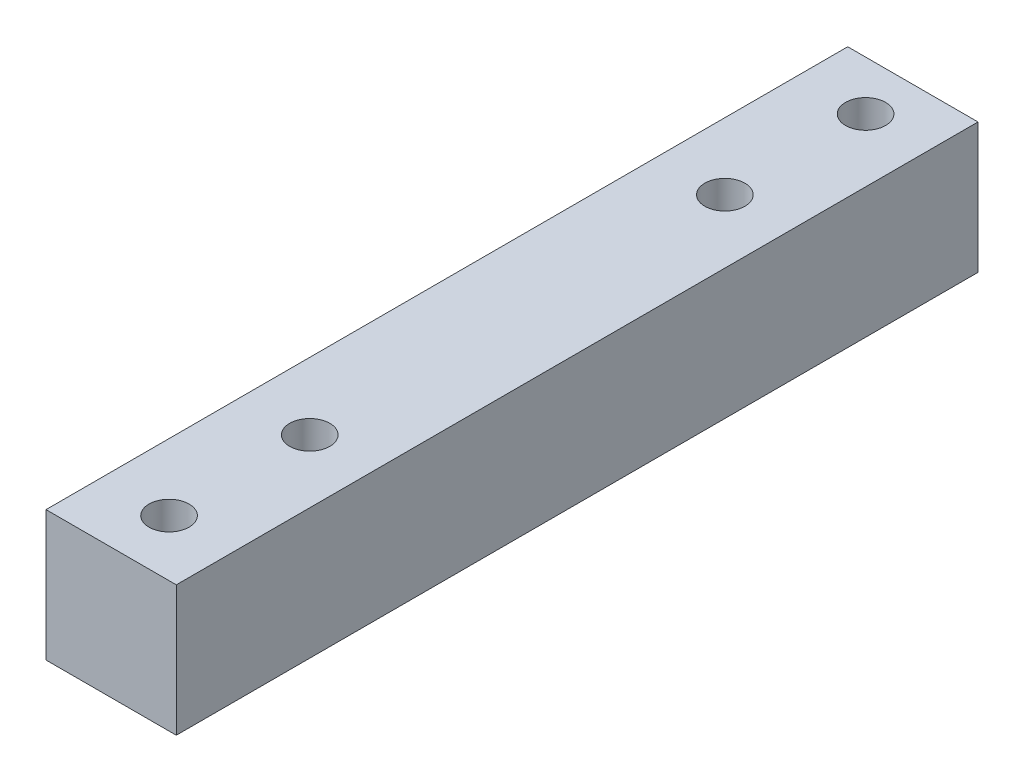
SolidWorks part; units mm, degrees
ref_plane "Front Plane" through (0, 0, 0) normal (0, 0, 1) x (1, 0, 0)
ref_plane "Top Plane" through (0, 0, 0) normal (0, 1, 0) x (1, 0, 0)
ref_plane "Right Plane" through (0, 0, 0) normal (1, 0, 0) x (0, 0, -1)
sketch "Sketch1" plane through (0, 0, 0) normal (0, 0, 1) x (1, 0, 0)
  line L1 (-6.5, 6.8095) -> (6.5, 6.8095)
  line L2 (-6.5, 6.8095) -> (-6.5, -6.1905)
  line L3 (-6.5, -6.1905) -> (6.5, -6.1905)
  line L4 (6.5, 6.8095) -> (6.5, -6.1905)
  line L5 (-6.5, 6.8095) -> (6.5, -6.1905) construction
  line L6 (-6.5, -6.1905) -> (6.5, 6.8095) construction
  point P0 (0, 0.3095)
  dimension "D1" = 13
  dimension "D2" = 13
extrude "Boss-Extrude1" add sketch "Sketch1" along normal blind 80
sketch "Sketch2" plane through (0, 6.8095, 0) normal (0, 1, 0) x (1, 0, 0)
  circle A0 centre (0.1978, -4.9169) radius 2
  circle A1 centre (0.1575, -18.9169) radius 2
  circle A2 centre (0.1978, -60.3793) radius 2
  circle A3 centre (0.1575, -74.3793) radius 2
  point P4 (-0.8106, -17.8245)
  point P5 (4.4331, -19.8413)
  dimension "D1" = 4
  dimension "D2" = 4
  dimension "D4" = 4
  dimension "D5" = 4
  dimension "D3" = 14
extrude "Cut-Extrude1" cut sketch "Sketch2" against normal blind 80
